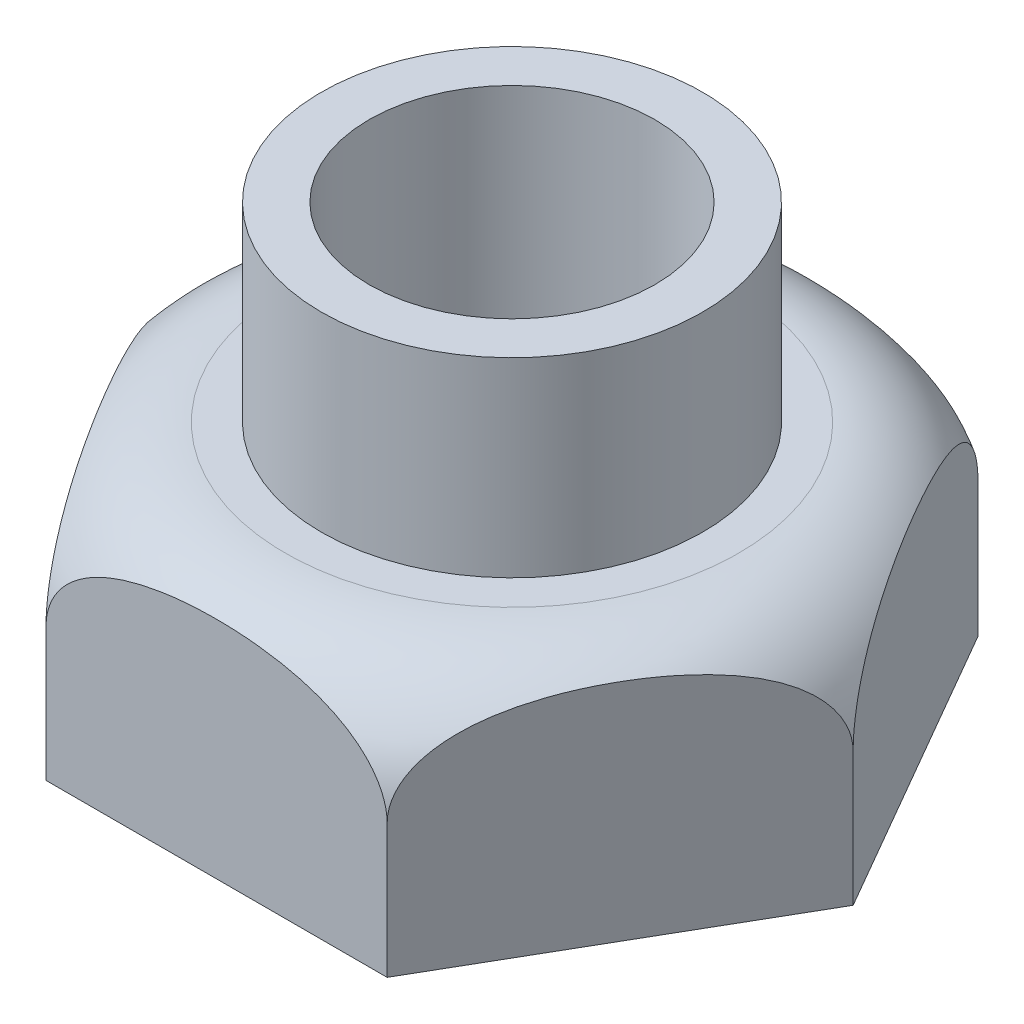
SolidWorks part; units mm, degrees
ref_plane "Front Plane" through (0, 0, 0) normal (0, 0, 1) x (1, 0, 0)
ref_plane "Top Plane" through (0, 0, 0) normal (0, 1, 0) x (1, 0, 0)
ref_plane "Right Plane" through (0, 0, 0) normal (1, 0, 0) x (0, 0, -1)
sketch "Sketch1" plane through (0, 0, 0) normal (0, 1, 0) x (1, 0, 0)
  line L1 (-89.4893, 0) -> (-44.7446, -77.5)
  line L2 (-44.7446, -77.5) -> (44.7446, -77.5)
  line L3 (44.7446, -77.5) -> (89.4893, 0)
  line L4 (89.4893, 0) -> (44.7446, 77.5)
  line L5 (44.7446, 77.5) -> (-44.7446, 77.5)
  line L6 (-44.7446, 77.5) -> (-89.4893, 0)
  circle A0 centre (0, 0) radius 77.5 construction
  dimension "D1" = 155
extrude "Boss-Extrude1" add sketch "Sketch1" along normal mid plane 65
sketch "Sketch2" plane through (0, 0, 0) normal (0, 0, 1) x (1, 0, 0)
  line L0 (-59.4893, 32.5) -> (-57.9514, 32.5)
  line L1 (-89.4893, 32.5) -> (-44.7446, 32.5) construction
  line L2 (-57.9514, 32.5) -> (-79.2458, 59.7807)
  line L3 (-79.2458, 59.7807) -> (-106.2191, 23.0515)
  line L4 (-106.2191, 23.0515) -> (-89.4893, -3.939)
  line L5 (-89.4893, 32.5) -> (-89.4893, -32.5) construction
  line L6 (-89.4893, -3.939) -> (-89.4893, 2.5)
  line L7 (0, 0) -> (0, 44.4498) construction
  arc A0 (-59.4893, 32.5) -> (-89.4893, 2.5) centre (-59.4893, 2.5) ccw
  point P12 (-89.4893, 32.5)
  dimension "D1" = 30
revolve "Cut-Revolve1" cut sketch "Sketch2" angle 360 about L7
sketch "Sketch3" plane through (0, 32.5, 0) normal (0, 1, 0) x (1, 0, 0)
  circle A0 centre (0, 0) radius 50
  circle A1 centre (0, 0) radius 37.5
  dimension "D1" = 100
  dimension "D2" = 75
extrude "Boss-Extrude2" add sketch "Sketch3" along normal blind 50
sketch "Sketch4" plane through (0, 32.5, 0) normal (0, 1, 0) x (1, 0, 0)
  circle A0 centre (0, 0) radius 37.5
  dimension "D1" = 75
extrude "Cut-Extrude1" cut sketch "Sketch4" against normal blind 94
